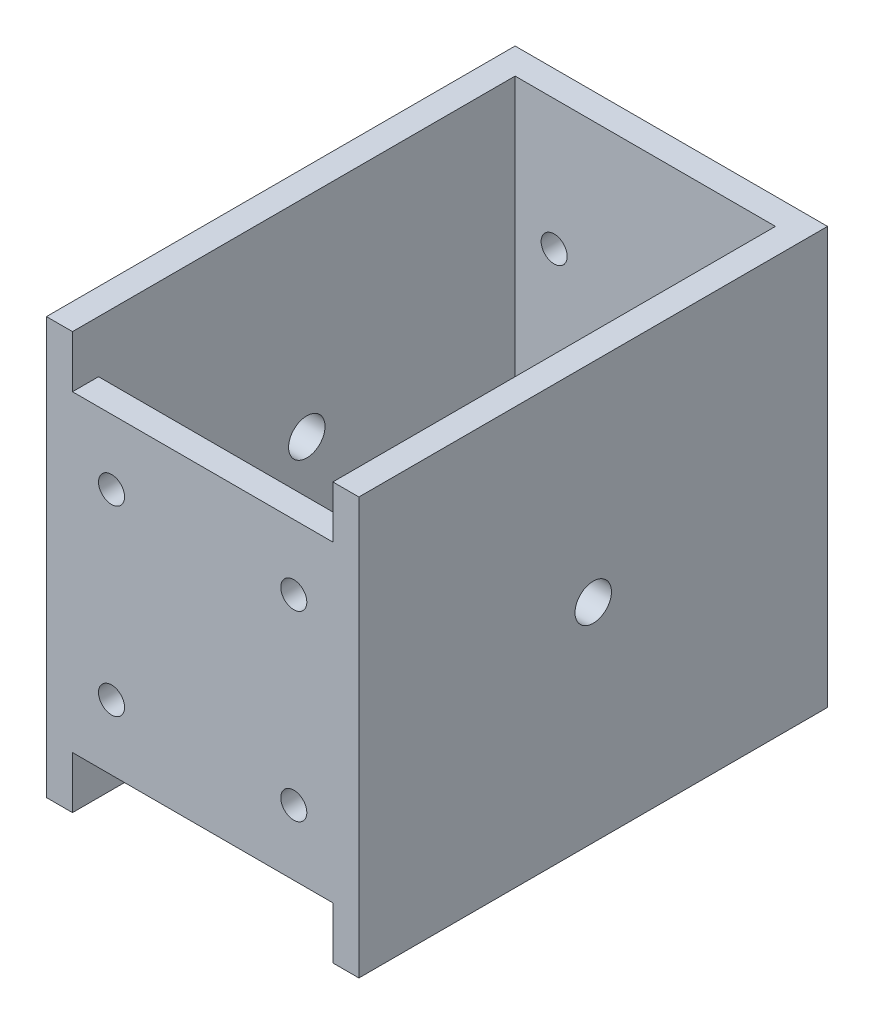
SolidWorks part; units mm, degrees
material "5052-H32"
ref_plane "Front Plane" through (0, 0, 0) normal (0, 0, 1) x (1, 0, 0)
ref_plane "Top Plane" through (0, 0, 0) normal (0, 1, 0) x (1, 0, 0)
ref_plane "Right Plane" through (0, 0, 0) normal (1, 0, 0) x (0, 0, -1)
sketch "Sketch1" plane through (0, 0, 0) normal (0, 0, 1) x (1, 0, 0)
  line L1 (-30, 40) -> (30, 40)
  line L2 (-30, 40) -> (-30, -40)
  line L3 (-30, -40) -> (30, -40)
  line L4 (30, 40) -> (30, -40)
  line L5 (-30, 40) -> (30, -40) construction
  line L6 (-30, -40) -> (30, 40) construction
  point P0 (0, 0)
  dimension "D1" = 60
  dimension "D2" = 80
extrude "Boss-Extrude1" add sketch "Sketch1" along normal blind 80
sketch "Sketch2" plane through (0, 40, 0) normal (0, 1, 0) x (1, 0, 0)
  line L0 (-25, -80) -> (-25, -5)
  line L1 (30, -80) -> (-30, -80) construction
  line L2 (-25, -5) -> (25, -5)
  line L3 (25, -5) -> (25, -80)
  line L4 (25, -80) -> (-25, -80)
  line L5 (30, -80) -> (30, 0) construction
  dimension "D1" = 75
  dimension "D2" = 50
  dimension "D3" = 5
extrude "Cut-Extrude1" cut sketch "Sketch2" against normal blind 80
sketch "Sketch3" plane through (0, 0, 0) normal (0, 0, -1) x (-1, 0, 0)
  line L1 (30, -40) -> (-30, -40) construction
  line L2 (-30, -40) -> (-30, 40) construction
  line L3 (30, 40) -> (30, -40) construction
  circle A0 centre (-17.5, 15) radius 2.5
  circle A1 centre (17.5, 15) radius 2.5
  circle A2 centre (-17.5, -20) radius 2.5
  circle A3 centre (17.5, -20) radius 2.5
  dimension "D1" = 5
  dimension "D2" = 5
  dimension "D3" = 5
  dimension "D4" = 5
  dimension "D5" = 20
  dimension "D6" = 12.5
  dimension "D7" = 20
  dimension "D8" = 12.5
  dimension "D9" = 12.5
  dimension "D10" = 35
  dimension "D11" = 12.5
  dimension "D12" = 35
extrude "Cut-Extrude2" cut sketch "Sketch3" against normal blind 60
sketch "Sketch4" plane through (30, 0, 0) normal (1, 0, 0) x (0, 0, -1)
  line L0 (0, -40) -> (0, 40) construction
  line L1 (-80, -40) -> (0, -40) construction
  circle A0 centre (-45, 0) radius 3.5
  point P8 (-40.4724, 0.3149)
  dimension "D1" = 7
  dimension "D2" = 45
  dimension "D3" = 40
extrude "Cut-Extrude3" cut sketch "Sketch4" against normal blind 80
sketch "Sketch5" plane through (0, 0, 80) normal (0, 0, 1) x (1, 0, 0)
  line L0 (-30, 40) -> (-25, 40)
  line L1 (-25, 40) -> (-25, -40)
  line L2 (-25, -40) -> (-30, -40)
  line L3 (-30, -40) -> (-30, 40)
  line L4 (25, 40) -> (30, 40)
  line L5 (30, 40) -> (30, -40)
  line L6 (30, -40) -> (25, -40)
  line L7 (25, -40) -> (25, 40)
extrude "Boss-Extrude2" add sketch "Sketch5" along normal blind 5
sketch "Sketch6" plane through (0, 0, 85) normal (0, 0, 1) x (1, 0, 0)
  line L0 (-30, 40) -> (30, 40)
  line L1 (30, 40) -> (30, -40)
  line L2 (30, -40) -> (-30, -40)
  line L3 (-30, -40) -> (-30, 40)
extrude "Boss-Extrude3" add sketch "Sketch6" along normal blind 5
sketch "Sketch7" plane through (0, 0, 90) normal (0, 0, 1) x (1, 0, 0)
  circle A0 centre (-17.5, 17.5) radius 2.5
  circle A1 centre (17.5, 17.5) radius 2.5
  circle A2 centre (17.5, -17.5) radius 2.5
  circle A3 centre (-17.5, -17.5) radius 2.5
  dimension "D1" = 5
  dimension "D2" = 5
  dimension "D3" = 5
  dimension "D4" = 5
  dimension "D5" = 17.5
  dimension "D6" = 17.5
  dimension "D7" = 35
  dimension "D8" = 35
  dimension "D9" = 35
  dimension "D10" = 35
  dimension "D11" = 17.5
  dimension "D12" = 17.5
extrude "Cut-Extrude4" cut sketch "Sketch7" against normal blind 5
sketch "Sketch8" plane through (0, 0, 90) normal (0, 0, 1) x (1, 0, 0)
  line L0 (-25, 40) -> (25, 40)
  line L1 (25, 40) -> (25, 30)
  line L2 (25, 30) -> (-25, 30)
  line L3 (-25, 30) -> (-25, 40)
  line L4 (-25, -40) -> (-25, -30)
  line L5 (-30, -40) -> (30, -40) construction
  line L6 (-25, -30) -> (25, -30)
  line L7 (25, -30) -> (25, -40)
  line L8 (25, -40) -> (-25, -40)
  dimension "D1" = 10
  dimension "D2" = 10
extrude "Cut-Extrude5" cut sketch "Sketch8" against normal blind 5
